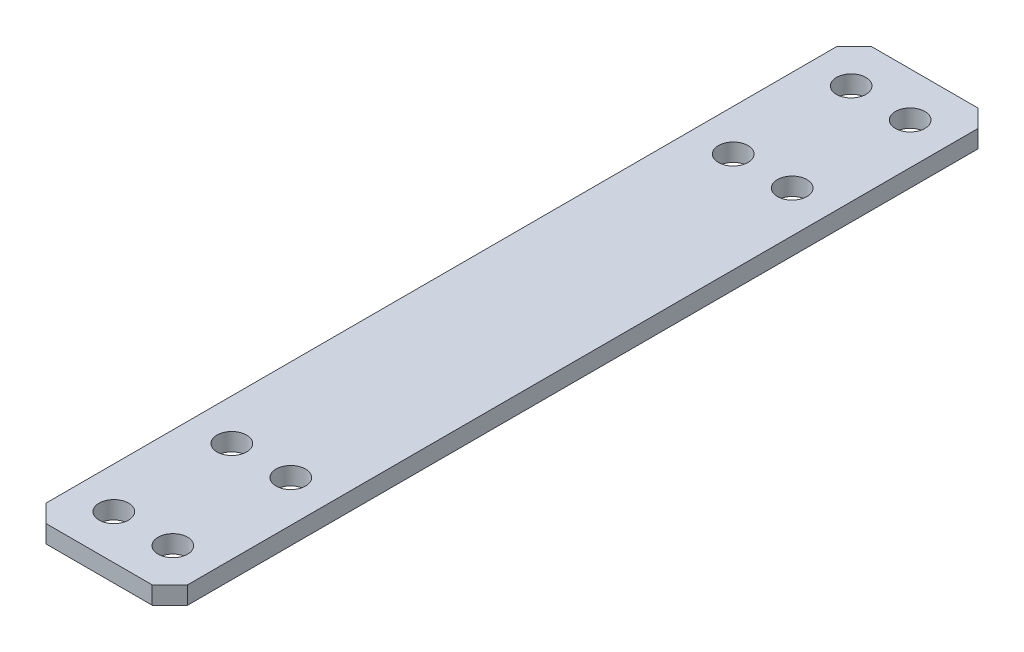
SolidWorks part; units mm, degrees
ref_plane "前基準面" through (0, 0, 0) normal (0, 0, 1) x (1, 0, 0)
ref_plane "上基準面" through (0, 0, 0) normal (0, 1, 0) x (1, 0, 0)
ref_plane "右基準面" through (0, 0, 0) normal (1, 0, 0) x (0, 0, -1)
ref_plane "平面1" through (0, 3, 0) normal (0, 1, 0) x (1, 0, 0)
sketch "草圖1" plane through (0, 3, 0) normal (0, 1, 0) x (1, 0, 0)
  line L0 (-12, 67) -> (-12, -67)
  line L1 (-12, -67) -> (-9, -70)
  line L2 (-9, -70) -> (9, -70)
  line L3 (9, -70) -> (12, -67)
  line L4 (12, -67) -> (12, 67)
  line L5 (12, 67) -> (9, 70)
  line L6 (9, 70) -> (-9, 70)
  line L7 (-9, 70) -> (-12, 67)
  circle A0 centre (-5, 62.5) radius 2.5
  circle A1 centre (5, 62.5) radius 2.5
  circle A2 centre (5, 42.5) radius 2.5
  circle A3 centre (-5, 42.5) radius 2.5
  circle A4 centre (5, -42.5) radius 2.5
  circle A5 centre (-5, -42.5) radius 2.5
  circle A6 centre (5, -62.5) radius 2.5
  circle A7 centre (-5, -62.5) radius 2.5
extrude "填料-伸長1" add sketch "草圖1" against normal blind 3
